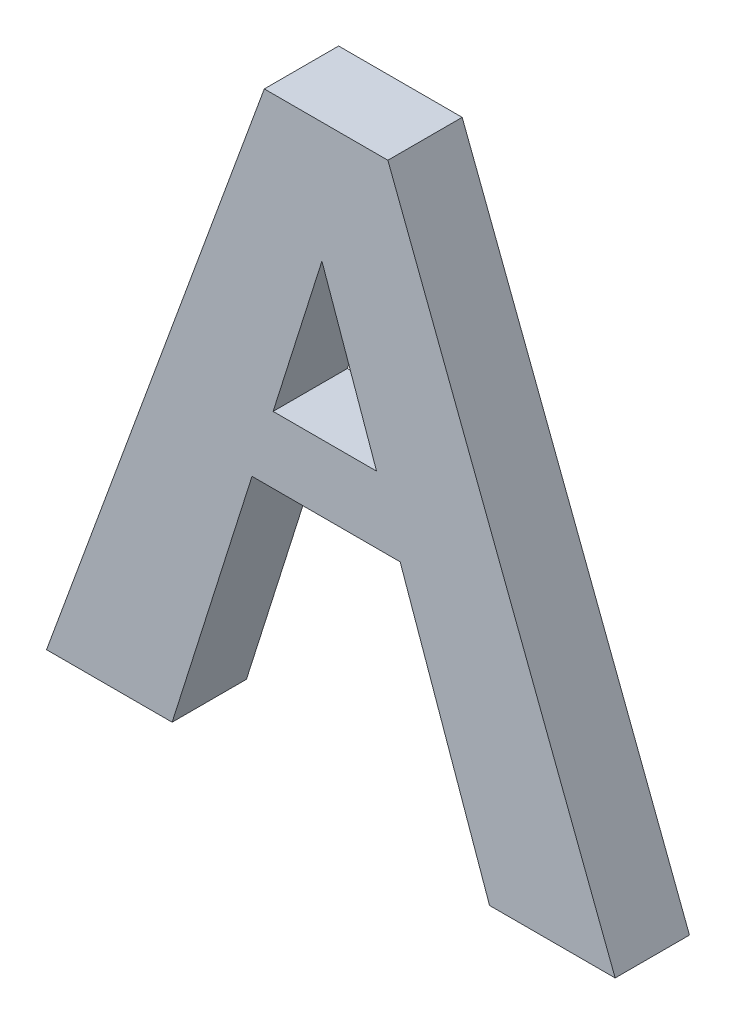
SolidWorks part; units mm, degrees
ref_plane "Front Plane" through (0, 0, 0) normal (0, 0, 1) x (1, 0, 0)
ref_plane "Top Plane" through (0, 0, 0) normal (0, 1, 0) x (1, 0, 0)
ref_plane "Right Plane" through (0, 0, 0) normal (1, 0, 0) x (0, 0, -1)
sketch "Sketch1" plane through (0, 0, 0) normal (0, 0, 1) x (1, 0, 0)
  line L0 (-5.2784, 29.1909) -> (5.2784, 29.1909)
  line L1 (5.2784, 29.1909) -> (24.6989, -21.6091)
  line L2 (24.6989, -21.6091) -> (13.9667, -21.6091)
  line L3 (13.9667, -21.6091) -> (6.3284, 0)
  line L4 (6.3284, 0) -> (-6.3284, 0)
  line L5 (-6.3284, 0) -> (-13.154, -21.6091)
  line L6 (-13.154, -21.6091) -> (-23.8863, -21.6091)
  line L7 (-23.8863, -21.6091) -> (-5.2784, 29.1909)
  line L9 (-0.3556, 18.9091) -> (4.3123, 5.7036)
  line L10 (4.3123, 5.7036) -> (-4.5268, 5.7036)
  line L11 (-4.5268, 5.7036) -> (-0.3556, 18.9091)
  point P11 (0, 0)
  point P14 (0, 29.1909)
  dimension "D1" = 50.8
extrude "Boss-Extrude1" add sketch "Sketch1" along normal mid plane 6.35
